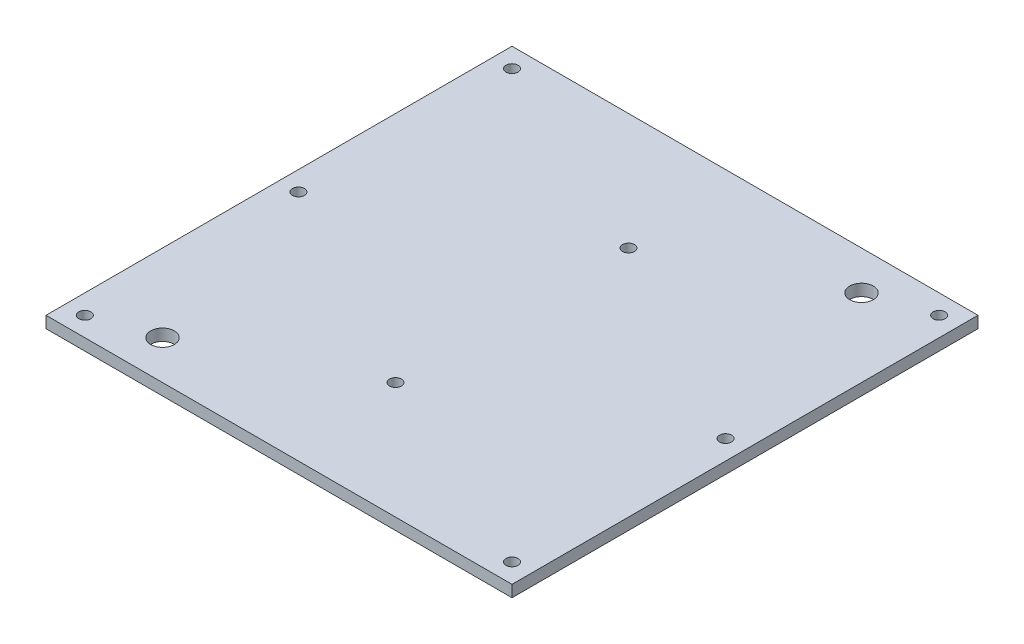
SolidWorks part; units mm, degrees
material "Pine"
ref_plane "Front Plane" through (0, 0, 0) normal (0, 0, 1) x (1, 0, 0)
ref_plane "Top Plane" through (0, 0, 0) normal (0, 1, 0) x (1, 0, 0)
ref_plane "Right Plane" through (0, 0, 0) normal (1, 0, 0) x (0, 0, -1)
sketch "Sketch1" plane through (0, 0, 0) normal (0, 1, 0) x (1, 0, 0)
  line L1 (-60, -60) -> (60, -60)
  line L2 (-60, -60) -> (-60, 60)
  line L3 (-60, 60) -> (60, 60)
  line L4 (60, -60) -> (60, 60)
  line L5 (0, 60) -> (0, -60) construction
  line L6 (-60, 0) -> (60, 0) construction
  circle A0 centre (0, 30) radius 1.55
  circle A1 centre (0, -30) radius 1.55
  circle A2 centre (-55, -55) radius 1.55
  circle A3 centre (55, -55) radius 1.55
  circle A4 centre (55, 55) radius 1.55
  circle A5 centre (-55, 55) radius 1.55
  circle A6 centre (-55, 0) radius 1.55
  circle A7 centre (55, 0) radius 1.55
  circle A8 centre (-40, -50) radius 3.05
  circle A9 centre (40, 50) radius 3.05
  point P0 (0, 0)
  dimension "D3" = 3.1
  dimension "D5" = 3.1
  dimension "D8" = 3.1
  dimension "D10" = 6.1
  dimension "D1" = 120
  dimension "D2" = 120
  dimension "D4" = 60
  dimension "D6" = 5
  dimension "D7" = 5
  dimension "D9" = 110
  dimension "D11" = 10
  dimension "D12" = 20
  dimension "D13" = 20
  dimension "D14" = 10
extrude "Boss-Extrude1" add sketch "Sketch1" along normal blind 3
